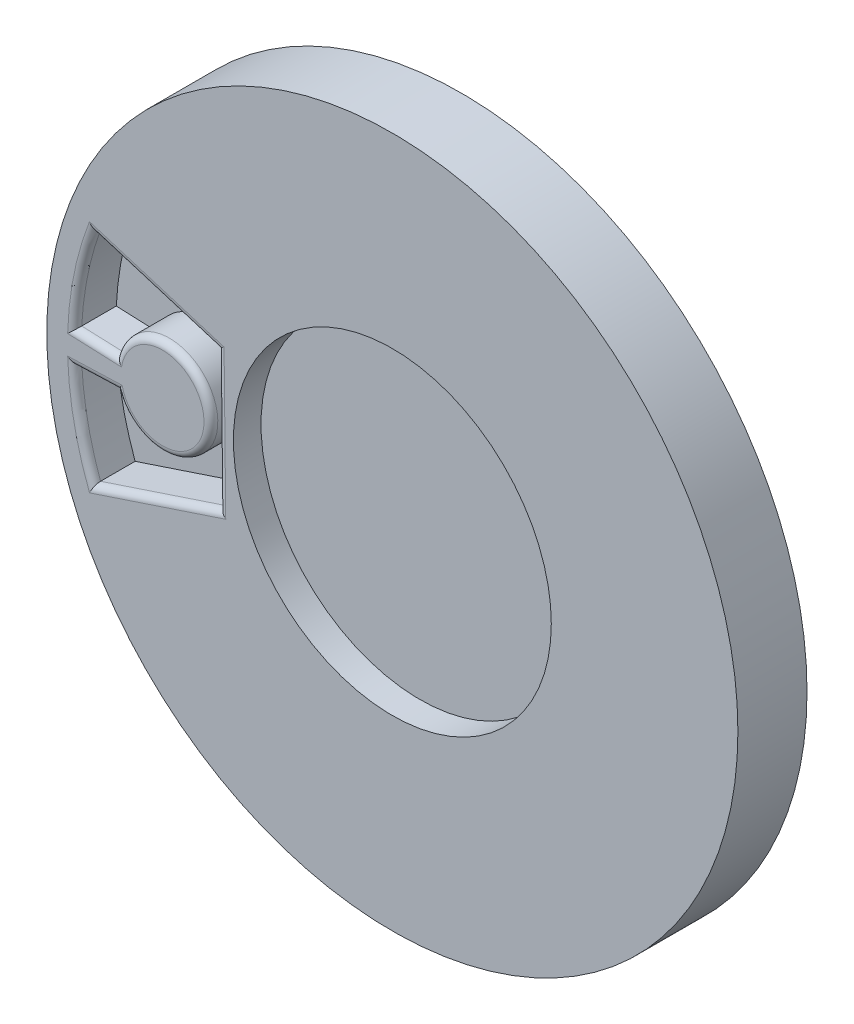
SolidWorks part; units mm, degrees
ref_plane "Front Plane" through (0, 0, 0) normal (0, 0, 1) x (1, 0, 0)
ref_plane "Top Plane" through (0, 0, 0) normal (0, 1, 0) x (1, 0, 0)
ref_plane "Right Plane" through (0, 0, 0) normal (1, 0, 0) x (0, 0, -1)
sketch "Sketch1" plane through (0, 0, 0) normal (0, 0, 1) x (1, 0, 0)
  circle A0 centre (0, 0) radius 25
  dimension "D1" = 50
extrude "Boss-Extrude1" add sketch "Sketch1" along normal blind 5
sketch "Sketch2" plane through (0, 0, 0) normal (0, 0, 1) x (1, 0, 0)
  line L2 (-19.9206, -1.095) -> (-22.9685, -1.2027)
  line L3 (-19.9903, 1.0511) -> (-22.9701, 1.1719)
  line L8 (-21.6098, -7.8752) -> (-12.5558, -4.8686)
  line L9 (-21.6093, 7.8764) -> (-12.6699, 5.1333)
  line L11 (-12.5558, -4.8686) -> (-12.6699, 5.1333)
  arc A0 (-21.6093, 7.8764) -> (-22.9701, 1.1719) centre (0, 0) ccw
  arc A1 (-22.9685, -1.2027) -> (-21.6098, -7.8752) centre (0, 0) ccw
  arc A10 (-19.9206, -1.095) -> (-19.9903, 1.0511) centre (-16.6259, 0.0862) ccw
extrude "Cut-Extrude1" cut sketch "Sketch2" against normal blind 3 from surface at 5 starting at face at (25, 0, 5)
sketch "Sketch3" plane through (0, 0, 0) normal (0, 0, 1) x (1, 0, 0)
  circle A0 centre (0, 0) radius 11.5
  dimension "D1" = 23
extrude "Cut-Extrude2" cut sketch "Sketch3" against normal blind 2 from surface at 5 starting at face at (-18.4957, 0.0516, 5)
sketch "Sketch4" plane through (0, 0, 0) normal (0, 0, 1) x (1, 0, 0)
  circle A0 centre (0, 0) radius 4
  dimension "D1" = 8
extrude "Boss-Extrude2" add sketch "Sketch4" against normal blind 10 from surface at 0 starting at face at (25, 0, 0)
sketch "Sketch5" plane through (0, 0, 0) normal (0, 0, 1) x (1, 0, 0)
  line L0 (-0.6, -5) -> (0.6, 5) construction
  line L1 (-0.6, 5) -> (0.6, -5) construction
  line L2 (-0.6, -5) -> (0.6, -5)
  line L3 (-0.6, 5) -> (0.6, 5)
  line L4 (-0.6, 5) -> (-0.6, -5)
  line L5 (0.6, -5) -> (0.6, 5)
  point P4 (0, 0)
  dimension "D1" = 1.2
  dimension "D2" = 10
extrude "Cut-Extrude3" cut sketch "Sketch5" along normal blind 5 from surface at -10 starting at face at (4, 0, -10)
fillet "Fillet1" radius 0.5 8 edges at (-13.1277, 0.1998, 5) (-21.4446, -1.1488, 5) (-21.4802, 1.1115, 5) (-22.5404, 4.575, 5) (-17.1396, 6.5048, 5) (-12.6128, 0.1323, 5) (-17.0828, -6.3719, 5) (-22.5374, -4.5895, 5)
